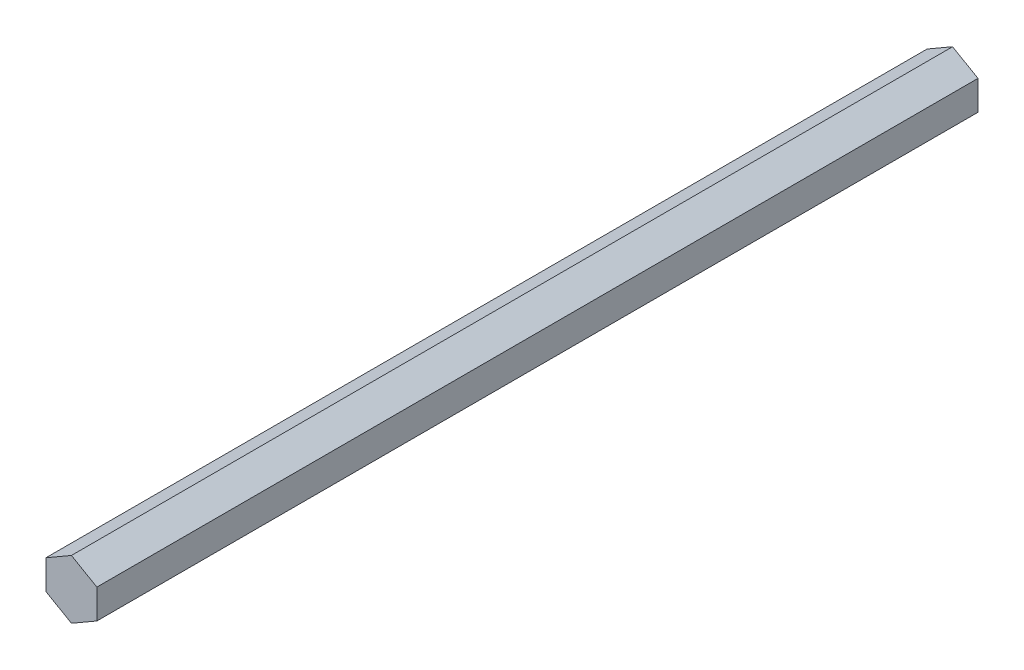
SolidWorks part; units mm, degrees
ref_plane "Front Plane" through (0, 0, 0) normal (0, 0, 1) x (1, 0, 0)
ref_plane "Top Plane" through (0, 0, 0) normal (0, 1, 0) x (1, 0, 0)
ref_plane "Right Plane" through (0, 0, 0) normal (1, 0, 0) x (0, 0, -1)
sketch "Sketch1" plane through (0, 0, 0) normal (0, 0, 1) x (1, 0, 0)
  line L1 (0, 7.3323) -> (-6.35, 3.6662)
  line L2 (-6.35, 3.6662) -> (-6.35, -3.6662)
  line L3 (-6.35, -3.6662) -> (0, -7.3323)
  line L4 (0, -7.3323) -> (6.35, -3.6662)
  line L5 (6.35, -3.6662) -> (6.35, 3.6662)
  line L6 (6.35, 3.6662) -> (0, 7.3323)
  circle A0 centre (0, 0) radius 6.35 construction
  dimension "D1" = 12.7
extrude "Boss-Extrude1" add sketch "Sketch1" along normal blind 220
